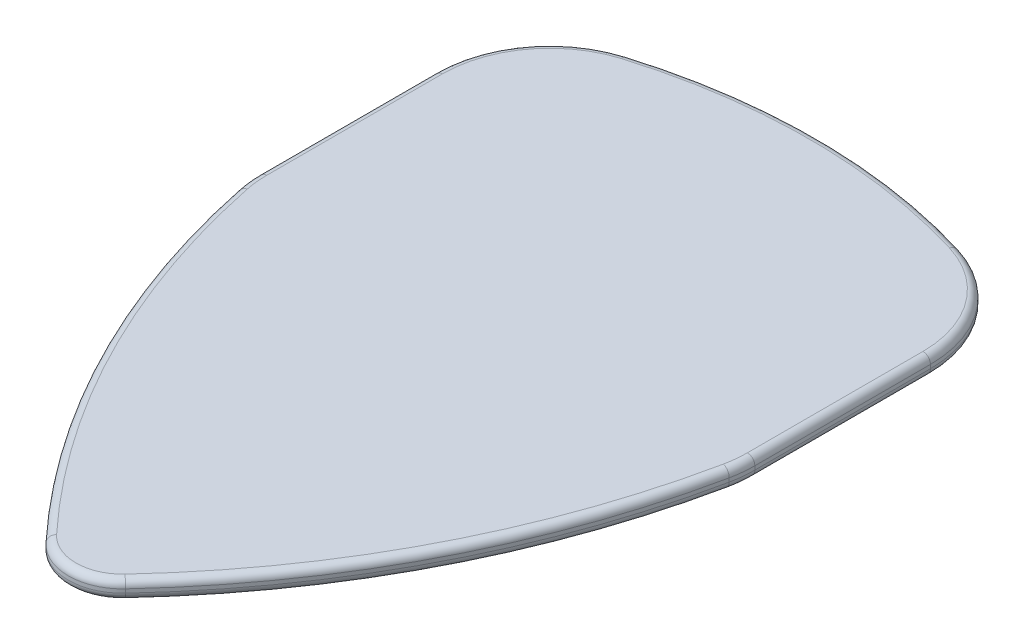
SolidWorks part; units mm, degrees
ref_plane "Front Plane" through (0, 0, 0) normal (0, 0, 1) x (1, 0, 0)
ref_plane "Top Plane" through (0, 0, 0) normal (0, 1, 0) x (1, 0, 0)
ref_plane "Right Plane" through (0, 0, 0) normal (1, 0, 0) x (0, 0, -1)
sketch "Sketch1" plane through (0, 0, 0) normal (0, 1, 0) x (1, 0, 0)
  line L0 (0, 0) -> (0, 30.62) construction
  line L1 (-13.11, 22.1848) -> (0, 22.1848) construction
  line L2 (0, 22.1848) -> (13.11, 22.1848) construction
  line L3 (0, 2.9) -> (-2.9, 2.9) construction
  line L6 (9.0762, 10.7993) -> (9.4821, 11.5846) construction
  line L7 (-7.0973, 23.4286) -> (-12.0562, 27.0493) construction
  arc A0 (-8.8774, 29.3049) -> (8.8774, 29.3049) centre (0, 0) cw
  arc A1 (-2.1219, 0.9232) -> (-13.11, 22.1848) centre (30.3499, 31.175) cw
  arc A2 (-13.11, 22.1848) -> (-8.8774, 29.3049) centre (-7.0973, 23.4286) cw
  arc A3 (2.1219, 0.9232) -> (13.11, 22.1848) centre (-30.3499, 31.175) ccw
  arc A4 (13.11, 22.1848) -> (8.8774, 29.3049) centre (7.0973, 23.4286) ccw
  arc A5 (-2.1219, 0.9232) -> (2.1219, 0.9232) centre (0, 2.9) ccw
  circle A6 centre (-7.0973, 23.4286) radius 6.14 construction
  circle A7 centre (-30.3499, 31.175) radius 44.38 construction
  circle A8 centre (0, 2.9) radius 2.9 construction
  point P8 (0, 30.62)
  dimension "D1" = 30.62
  dimension "D2" = 26.22
  dimension "D3" = 44.38
  dimension "D4" = 6.14
  dimension "D5" = 2.9
extrude "Boss-Extrude1" add sketch "Sketch1" along normal blind 1
sketch "Sketch2" plane through (0, 0, 0) normal (0, 1, 0) x (1, 0, 0)
  line L0 (-13.2373, 32.8086) -> (-13.2373, 23.4286)
  line L1 (13.2373, 32.8086) -> (13.2373, 23.4286)
  line L2 (0, 30.62) -> (0, 40) construction
  line L3 (-8.8774, 38.6849) -> (8.8774, 38.6849) construction
  line L4 (-13.2373, 23.4286) -> (13.2373, 23.4286)
  arc A0 (-8.8774, 29.3049) -> (-13.11, 22.1848) centre (-7.0973, 23.4286) ccw construction
  arc A1 (13.11, 22.1848) -> (8.8774, 29.3049) centre (7.0973, 23.4286) ccw construction
  arc A2 (-8.8774, 38.6849) -> (-13.2373, 32.8086) centre (-7.0973, 32.8086) ccw
  arc A3 (8.8774, 38.6849) -> (13.2373, 32.8086) centre (7.0973, 32.8086) ccw construction
  circle A4 centre (-7.0973, 23.4286) radius 6.14 construction
  arc A5 (-13.2373, 32.8086) -> (-8.8774, 38.6849) centre (-7.0973, 32.8086) ccw construction
  arc A6 (13.2373, 32.8086) -> (8.8774, 38.6849) centre (7.0973, 32.8086) ccw
  arc A7 (-8.8774, 38.6849) -> (8.8774, 38.6849) centre (0, 9.38) cw
  arc A8 (8.8774, 29.3049) -> (-8.8774, 29.3049) centre (0, 0) ccw construction
  point P16 (13.2345, 32.995)
  dimension "D1" = 40
extrude "Boss-Extrude2" add sketch "Sketch2" along normal blind 1 contours A7 A6 L1 L4 L0 A2
fillet "Fillet1" radius 0.4 20 edges at (-9.0762, 0, -10.7993) (0, 0, 0) (9.0762, 0, -10.7993) (13.2054, 0, -22.8034) (-13.2054, 0, -22.8034) (13.2054, 1, -22.8034) (9.0762, 1, -10.7993) (0, 1, 0) (-9.0762, 1, -10.7993) (-13.2054, 1, -22.8034) (13.2373, 0, -28.1186) (13.2373, 1, -28.1186) (12.0283, 0, -36.4671) (12.0283, 1, -36.4671) (0, 0, -40) (0, 1, -40) (-12.0283, 0, -36.4671) (-12.0283, 1, -36.4671) (-13.2373, 0, -28.1186) (-13.2373, 1, -28.1186)
